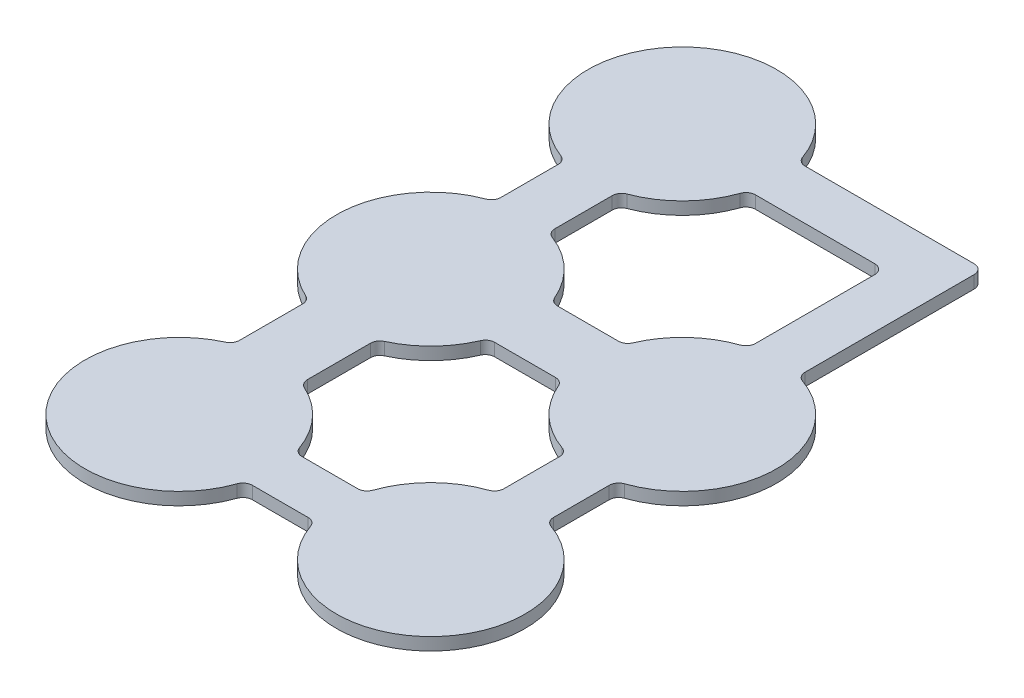
SolidWorks part; units mm, degrees
ref_plane "Front Plane" through (0, 0, 0) normal (0, 0, 1) x (1, 0, 0)
ref_plane "Top Plane" through (0, 0, 0) normal (0, 1, 0) x (1, 0, 0)
ref_plane "Right Plane" through (0, 0, 0) normal (1, 0, 0) x (0, 0, -1)
sketch "Sketch1" plane through (0, 0, 0) normal (0, 1, 0) x (1, 0, 0)
  line L0 (-10, 0) -> (10, 0) construction
  line L1 (-10, 0) -> (-10, 20) construction
  line L2 (-10, 0) -> (-10, -20) construction
  line L3 (-10, -20) -> (10, -20) construction
  line L4 (10, -20) -> (10, 0) construction
  line L6 (-12.15, 12.8148) -> (-7.85, 12.8148)
  line L7 (-12.15, 12.8148) -> (-12.15, 7.1852)
  line L8 (-12.15, 7.1852) -> (-7.85, 7.1852)
  line L9 (-7.85, 12.8148) -> (-7.85, 7.1852)
  line L14 (-12.7, -6.9971) -> (-7.3, -6.9971)
  line L15 (-12.7, -6.9971) -> (-12.7, -13.0029)
  line L16 (-12.7, -13.0029) -> (-7.3, -13.0029)
  line L17 (-7.3, -6.9971) -> (-7.3, -13.0029)
  line L18 (-2.7647, -18.025) -> (2.7647, -18.025)
  line L19 (-2.7647, -18.025) -> (-2.7647, -21.975)
  line L20 (-2.7647, -21.975) -> (2.7647, -21.975)
  line L21 (2.7647, -18.025) -> (2.7647, -21.975)
  line L22 (8.025, -7.2353) -> (11.975, -7.2353)
  line L23 (8.025, -7.2353) -> (8.025, -12.7647)
  line L24 (8.025, -12.7647) -> (11.975, -12.7647)
  line L25 (11.975, -7.2353) -> (11.975, -12.7647)
  line L26 (-2.9289, 2.5) -> (2.9289, 2.5)
  line L27 (-2.9289, 2.5) -> (-2.9289, -2.5)
  line L28 (-2.9289, -2.5) -> (2.9289, -2.5)
  line L29 (2.9289, 2.5) -> (2.9289, -2.5)
  line L30 (-2.7647, 21.975) -> (11.975, 21.975)
  line L31 (-2.7647, 21.975) -> (-2.7647, 18.025)
  line L32 (-2.7647, 18.025) -> (11.975, 18.025)
  line L33 (11.975, 21.975) -> (11.975, 18.025)
  line L34 (11.975, 7.2353) -> (8.025, 7.2353)
  line L35 (11.975, 7.2353) -> (11.975, 21.975)
  line L36 (11.975, 21.975) -> (8.025, 21.975)
  line L37 (8.025, 7.2353) -> (8.025, 21.975)
  circle A0 centre (10, 0) radius 7.5
  circle A1 centre (-10, 0) radius 7.5
  circle A2 centre (-10, 20) radius 7.5
  circle A3 centre (-10, -20) radius 7.5
  circle A4 centre (10, -20) radius 7.5
  point P10 (0, 0)
  point P15 (-10, 12.8148)
  point P33 (-10, -6.9971)
  point P34 (-2.7647, -20)
  point P35 (10, -7.2353)
  point P36 (-2.9289, 0)
  dimension "D1" = 15
  dimension "D2" = 20
  dimension "D3" = 4.3
  dimension "D4" = 5.4
  dimension "D5" = 5
  dimension "D6" = 3.95
  dimension "D7" = 3.95
  dimension "D8" = 3.95
extrude "Boss-Extrude1" add sketch "Sketch1" along normal blind 1 contours A3 L17 A1 L15 | A4 L18 A3 L20 | A4 L25 A0 L23 | A0 L35 L32 L37 | A1 L28 A0 L26 | L37 L32 L33 L30 | A2 L32 L37 L30 | A2 L7 A1 L9
fillet "Fillet1" radius 0.75 26 edges at (2.9289, 0.5, -2.5) (-2.9289, 0.5, -2.5) (11.975, 0.5, -21.975) (-2.7647, 0.5, -21.975) (8.025, 0.5, -7.2353) (11.975, 0.5, -7.2353) (11.975, 0.5, 12.7647) (2.7647, 0.5, 21.975) (-2.7647, 0.5, 21.975) (-2.7647, 0.5, 18.025) (2.7647, 0.5, 18.025) (8.025, 0.5, 12.7647) (11.975, 0.5, 7.2353) (-2.9289, 0.5, 2.5) (2.9289, 0.5, 2.5) (8.025, 0.5, 7.2353) (-12.7, 0.5, 13.0029) (-7.3, 0.5, 13.0029) (-7.3, 0.5, 6.9971) (-12.7, 0.5, 6.9971) (-12.15, 0.5, -7.1852) (-7.85, 0.5, -7.1852) (8.025, 0.5, -18.025) (-2.7647, 0.5, -18.025) (-7.85, 0.5, -12.8148) (-12.15, 0.5, -12.8148)
